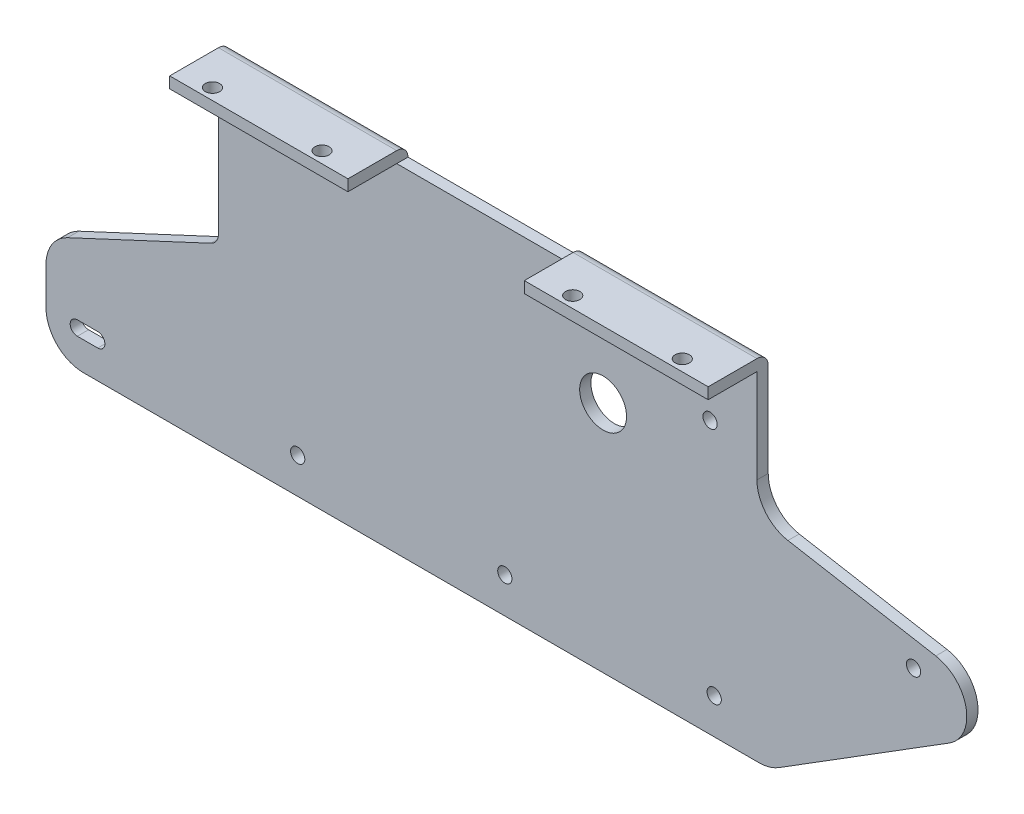
SolidWorks part; units mm, degrees
material "1060 Alloy"
ref_plane "Front Plane" through (0, 0, 0) normal (0, 0, 1) x (1, 0, 0)
ref_plane "Top Plane" through (0, 0, 0) normal (0, 1, 0) x (1, 0, 0)
ref_plane "Right Plane" through (0, 0, 0) normal (1, 0, 0) x (0, 0, -1)
sketch "Sketch1" plane through (0, 0, 0) normal (0, 0, 1) x (1, 0, 0)
  line L0 (0, 0) -> (143.5, 0)
  line L1 (143.5, 0) -> (143.5, -25)
  line L2 (151.7635, -34.8481) -> (191.1558, -41.794)
  line L3 (194.7185, -60.1226) -> (149.3364, -88.4805)
  line L4 (144.0372, -90) -> (-35.9628, -90)
  line L5 (-45.9628, -80) -> (-45.9628, -70)
  line L6 (-40.189, -60.9369) -> (-1.9907, -43.1248)
  line L7 (0, 0) -> (0, -40)
  arc A0 (-45.9628, -70) -> (-40.189, -60.9369) centre (-35.9628, -70) cw
  arc A1 (143.5, -25) -> (151.7635, -34.8481) centre (153.5, -25) ccw
  arc A2 (191.1558, -41.794) -> (194.7185, -60.1226) centre (189.4193, -51.6421) cw
  arc A3 (144.0372, -90) -> (149.3364, -88.4805) centre (144.0372, -80) ccw
  arc A4 (-45.9628, -80) -> (-35.9628, -90) centre (-35.9628, -80) ccw
  arc A5 (-1.9907, -43.1248) -> (0, -40) centre (-3.4478, -40) ccw
  dimension "D6" = 10
  dimension "D7" = 10
  dimension "D10" = 10
  dimension "D11" = 40
  dimension "D12" = 10
  dimension "D15" = 10
  dimension "D1" = 143.5
  dimension "D2" = 25
  dimension "D3" = 40
  dimension "D4" = 90
  dimension "D5" = 10
  dimension "D8" = 180
  dimension "D9" = 32
  dimension "D13" = 10
  dimension "D14" = 25
extrude "Boss-Extrude1" add sketch "Sketch1" along normal blind 3
sketch "Sketch2" plane through (0, 0, 3) normal (0, 0, 1) x (1, 0, 0)
  line L0 (-35.9628, -90) -> (144.0372, -90) construction
  line L3 (149.3364, -88.4805) -> (194.7185, -60.1226) construction
  line L4 (132.1078, -80.5) -> (132.1078, -90) construction
  line L5 (-35.9628, -90) -> (144.0372, -90) construction
  line L6 (132.1078, -80.5) -> (162.1078, -80.5) construction
  line L7 (132.1078, -80.5) -> (76.3078, -80.5) construction
  line L9 (21.1078, -80.5) -> (-32.1672, -80.5) construction
  line L10 (-32.1672, -80.5) -> (-37.6172, -80.5) construction
  line L11 (-32.1672, -82.4) -> (-37.6172, -82.4)
  line L12 (-32.1672, -78.6) -> (-37.6172, -78.6)
  line L13 (102.5, -27.75) -> (0, -27.75) construction
  line L14 (0, 0) -> (0, -40) construction
  line L15 (143.5, 0) -> (0, 0) construction
  circle A0 centre (185.2283, -47.5688) radius 1.9
  circle A2 centre (132.1078, -80.5) radius 1.9
  circle A3 centre (76.3078, -80.5) radius 1.9
  circle A4 centre (21.1078, -80.5) radius 1.9
  arc A5 (-32.1672, -82.4) -> (-32.1672, -78.6) centre (-32.1672, -80.5) ccw
  arc A6 (-37.6172, -78.6) -> (-37.6172, -82.4) centre (-37.6172, -80.5) ccw
  circle A7 centre (102.5, -27.75) radius 6.25
  circle A8 centre (131.0078, -17.5) radius 1.9
  point P22 (-34.8922, -80.5)
  dimension "D1" = 3.8
  dimension "D7" = 1.9
  dimension "D8" = 5.45
  dimension "D11" = 12.5
  dimension "D2" = 62
  dimension "D3" = 9.5
  dimension "D4" = 30
  dimension "D5" = 55.8
  dimension "D6" = 167
  dimension "D9" = 102.5
  dimension "D10" = 27.75
  dimension "D12" = 62.5
  dimension "D13" = 111
  dimension "D14" = 1.1
  dimension "D15" = 72.5
extrude "Cut-Extrude1" cut sketch "Sketch2" against normal through all contours A7 | A2 | A0 | A3 | A4 | L12 A6 L11 A5 | A8
sketch "Sketch3" plane through (143.5, 0, 0) normal (1, 0, 0) x (0, 0, -1)
  line L0 (0, 0) -> (-16, 0)
  line L1 (-3, 3) -> (-16, 3)
  line L2 (-16, 3) -> (-16, 0)
  line L3 (-3, 0) -> (0, 0)
  line L4 (-3, -25) -> (-3, 0) construction
  line L5 (-3, -25) -> (-3, 0)
  line L6 (0, -25) -> (0, 0) construction
  line L7 (0, -25) -> (0, 0)
  arc A2 (-3, 3) -> (0, 0) centre (-3, 0) cw
  line M10 (0, 0) -> (-3, 0)
  dimension "D1" = 3
  dimension "D2" = 16
extrude "Boss-Extrude3" add sketch "Sketch3" against normal up to surface (143.5 mm away) contours A2 L1 L2 L0 M10 up to face at (0, -20, 1.5)
sketch "Sketch6" plane through (0, 3, 0) normal (0, 1, 0) x (1, 0, 0)
  line L0 (47.5, 0) -> (94.5, 0)
  line L1 (143.5, 0) -> (0, 0) construction
  line L2 (94.5, 0) -> (94.5, -16)
  line L3 (0, -16) -> (143.5, -16) construction
  line L4 (94.5, -16) -> (47.5, -16)
  line L5 (47.5, -16) -> (47.5, 0)
  line L6 (0, -16) -> (0, -3) construction
  line L7 (143.5, -3) -> (143.5, -16) construction
  dimension "D1" = 47.5
  dimension "D2" = 49
extrude "Cut-Extrude4" cut sketch "Sketch6" against normal up to vertex (3 mm away)
sketch "Sketch7" plane through (0, 3, 0) normal (0, 1, 0) x (1, 0, 0)
  line L0 (0, -13) -> (143.5, -13) construction
  line L1 (0, -16) -> (0, -3) construction
  line L2 (143.5, -3) -> (143.5, -16) construction
  line L3 (0, -16) -> (47.5, -16) construction
  line L4 (94.5, -16) -> (94.5, -3) construction
  line L5 (47.5, -3) -> (47.5, -16) construction
  circle A0 centre (133.6, -13) radius 1.9
  circle A1 centre (104.4, -13) radius 1.9
  circle A2 centre (37.6, -13) radius 1.9
  circle A3 centre (8.4, -13) radius 1.9
  dimension "D6" = 3.8
  dimension "D1" = 3
  dimension "D2" = 9.9
  dimension "D3" = 9.9
  dimension "D4" = 9.9
  dimension "D5" = 8.4
extrude "Cut-Extrude5" cut sketch "Sketch7" against normal through all
